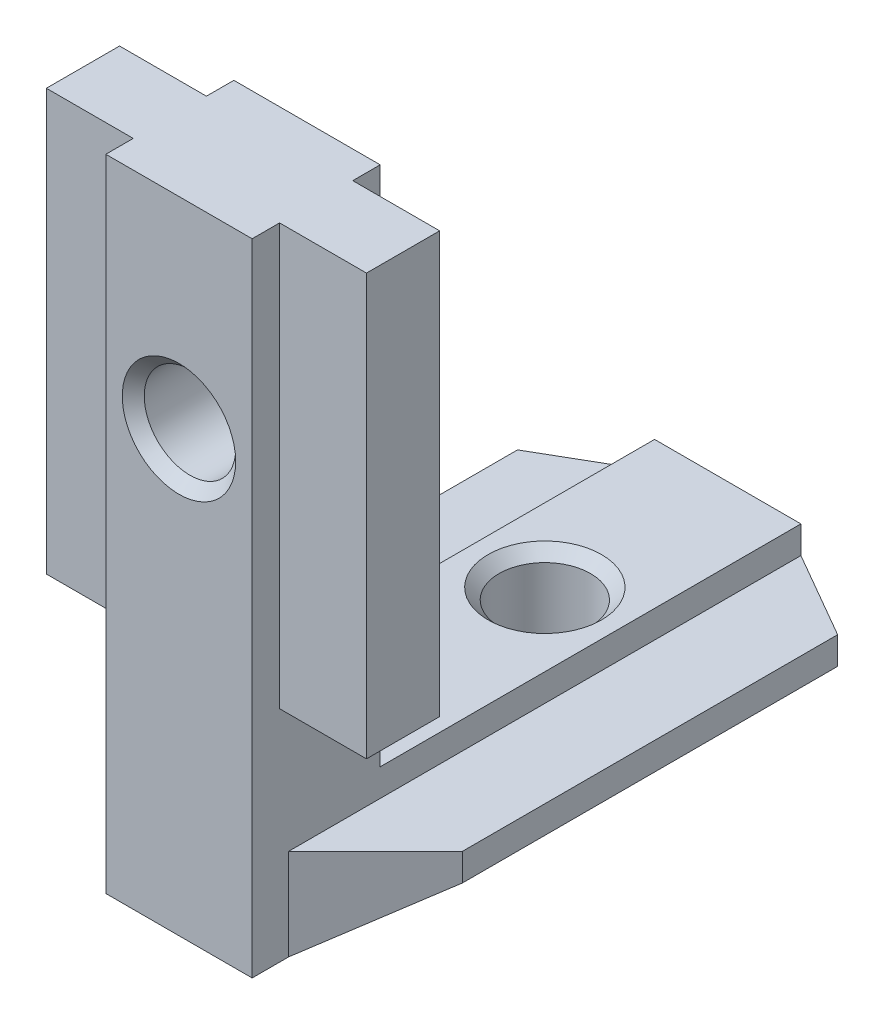
SolidWorks part; units mm, degrees
material "ЦА4М3 ГОСТ 25140-93"
ref_plane "Спереди" through (0, 0, 0) normal (0, 0, 1) x (1, 0, 0)
ref_plane "Сверху" through (0, 0, 0) normal (0, 1, 0) x (1, 0, 0)
ref_plane "Справа" through (0, 0, 0) normal (1, 0, 0) x (0, 0, -1)
sketch "Эскиз1" plane through (0, 0, 0) normal (0, 0, 1) x (1, 0, 0)
  line L0 (4, 0) -> (-4, 0)
  line L1 (-4, 0) -> (-4, -1.5)
  line L2 (-4, -1.5) -> (-8.75, -1.5)
  line L3 (-8.75, -1.5) -> (-8.75, -3)
  line L4 (-4, -6.5) -> (4, -6.5)
  line L5 (0, -6.5) -> (0, 0) construction
  line L7 (4, -1.5) -> (8.75, -1.5)
  line L8 (4, 0) -> (4, -1.5)
  line L9 (-8.75, -3) -> (-4, -6.5)
  line L10 (8.75, -3) -> (4, -6.5)
  line L11 (8.75, -1.5) -> (8.75, -3)
  dimension "D1" = 8
  dimension "D2" = 17.5
  dimension "D3" = 6.5
  dimension "D4" = 1.5
  dimension "D5" = 1.5
extrude "Бобышка-Вытянуть1" add sketch "Эскиз1" along normal blind 30
sketch "Эскиз2" plane through (0, 0, 0) normal (1, 0, 0) x (0, 0, -1)
  line L0 (-30, -6.5) -> (-30, 28.5)
  line L1 (-30, 28.5) -> (-23, 28.5)
  line L2 (-23, 28.5) -> (-23, -6.5)
  line L4 (-30, -6.5) -> (0, -6.5) construction
  line L5 (-23, -6.5) -> (-30, -6.5)
  dimension "D1" = 35
  dimension "D2" = 7
extrude "Бобышка-Вытянуть2" add sketch "Эскиз2" along normal mid plane 8
sketch "Эскиз3" plane through (0, -1.5, 0) normal (0, 1, 0) x (1, 0, 0)
  line L0 (-4, 0) -> (-8.75, -2.7424)
  line L1 (-8.75, -30) -> (-8.75, 0) construction
  line L2 (-8.75, -2.7424) -> (-8.75, 0)
  line L3 (-8.75, 0) -> (-4, 0)
  line L4 (-4, -28) -> (-8.75, -23.25)
  line L5 (-4, -30) -> (-4, 0) construction
  line L6 (-8.75, -23.25) -> (-8.75, -30)
  line L7 (-4, -30) -> (-8.75, -30) construction
  line L8 (-8.75, -30) -> (-4, -30)
  line L9 (-4, -30) -> (-4, -28)
  line L10 (0, 0) -> (0, -30) construction
  line L11 (4, 0) -> (-4, 0) construction
  line L12 (4, -30) -> (-4, -30) construction
  line L13 (4, -30) -> (4, -28)
  line L14 (8.75, -30) -> (4, -30)
  line L15 (8.75, -23.25) -> (8.75, -30)
  line L16 (4, -28) -> (8.75, -23.25)
  line L17 (8.75, 0) -> (4, 0)
  line L18 (8.75, -2.7424) -> (8.75, 0)
  line L19 (4, 0) -> (8.75, -2.7424)
  dimension "D1" = 2
  dimension "D2" = 45
  dimension "D3" = 30
extrude "Вырез-Вытянуть1" cut sketch "Эскиз3" against normal through all
sketch "Эскиз4" plane through (0, 28.5, 0) normal (0, 1, 0) x (1, 0, 0)
  line L0 (4, -23) -> (4, -30) construction
  line L1 (-8.75, -24.5) -> (8.75, -24.5)
  line L2 (-8.75, -24.5) -> (-8.75, -28.5)
  line L3 (-8.75, -28.5) -> (8.75, -28.5)
  line L4 (8.75, -24.5) -> (8.75, -28.5)
  line L5 (-8.75, -24.5) -> (8.75, -28.5) construction
  line L6 (-8.75, -28.5) -> (8.75, -24.5) construction
  point P0 (0, -26.5)
  point P9 (4, -26.5)
  dimension "D1" = 17.5
  dimension "D2" = 4
extrude "Бобышка-Вытянуть3" add sketch "Эскиз4" against normal blind 23
hole_wizard "Отверстие обработанное метчиком M61" positions "Эскиз5" profile "Эскиз6" tap size "M6" standard "ISO" end condition through all
sketch "Эскиз5" plane through (0, -6.5, 0) normal (0, -1, 0) x (-1, 0, 0)
  line L0 (4, 0) -> (-4, 0) construction
  point P0 (0, -10)
  dimension "D1" = 10
sketch "Эскиз6" plane through (0, -6.5, 10) normal (1, 0, 0) x (0, 0, -1)
  line L0 (0, 0) -> (0, 6.5)
  line L1 (0, 6.5) -> (3.1, 6.5)
  line L2 (2.5, 5.9) -> (2.5, 0.6)
  line L3 (2.5, 0.6) -> (3.1, 0)
  line L5 (3.1, 0) -> (0, 0)
  line L6 (-2.5, 0.6) -> (-3.1, 0) construction
  line L7 (3.1, 6.5) -> (2.5, 5.9)
  line L8 (-3.1, 6.5) -> (-2.5, 5.9) construction
  line L11 (0, -6.35) -> (0, 107.95) construction
  dimension "Диаметр проходного сверла" = 5
  dimension "Глубина проходного сверла" = 6.5
  dimension "Диаметр передней зенковки" = 6.2
  dimension "Угол передней зенковки" = 90
  dimension "Диаметр задней зенковки" = 6.2
  dimension "Угол задней зенковки" = 90
cosmetic thread "Отверстие резьбы1" parameters "D2"=6
hole_wizard "Отверстие обработанное метчиком M62" positions "Эскиз7" profile "Эскиз8" tap size "M6" standard "ISO" end condition through all
sketch "Эскиз7" plane through (0, 0, 30) normal (0, 0, 1) x (1, 0, 0)
  line L0 (-4, -6.5) -> (4, -6.5) construction
  point P0 (0, 17.5)
  dimension "D1" = 24
sketch "Эскиз8" plane through (0, 17.5, 30) normal (1, 0, 0) x (0, -1, 0)
  line L0 (0, 0) -> (0, 7)
  line L1 (0, 7) -> (3.1, 7)
  line L2 (2.5, 6.4) -> (2.5, 0.6)
  line L3 (2.5, 0.6) -> (3.1, 0)
  line L5 (3.1, 0) -> (0, 0)
  line L6 (-2.5, 0.6) -> (-3.1, 0) construction
  line L7 (3.1, 7) -> (2.5, 6.4)
  line L8 (-3.1, 7) -> (-2.5, 6.4) construction
  line L11 (0, -6.35) -> (0, 107.95) construction
  dimension "Диаметр проходного сверла" = 5
  dimension "Глубина проходного сверла" = 7
  dimension "Диаметр передней зенковки" = 6.2
  dimension "Угол передней зенковки" = 90
  dimension "Диаметр задней зенковки" = 6.2
  dimension "Угол задней зенковки" = 90
cosmetic thread "Отверстие резьбы2" parameters "D2"=6
